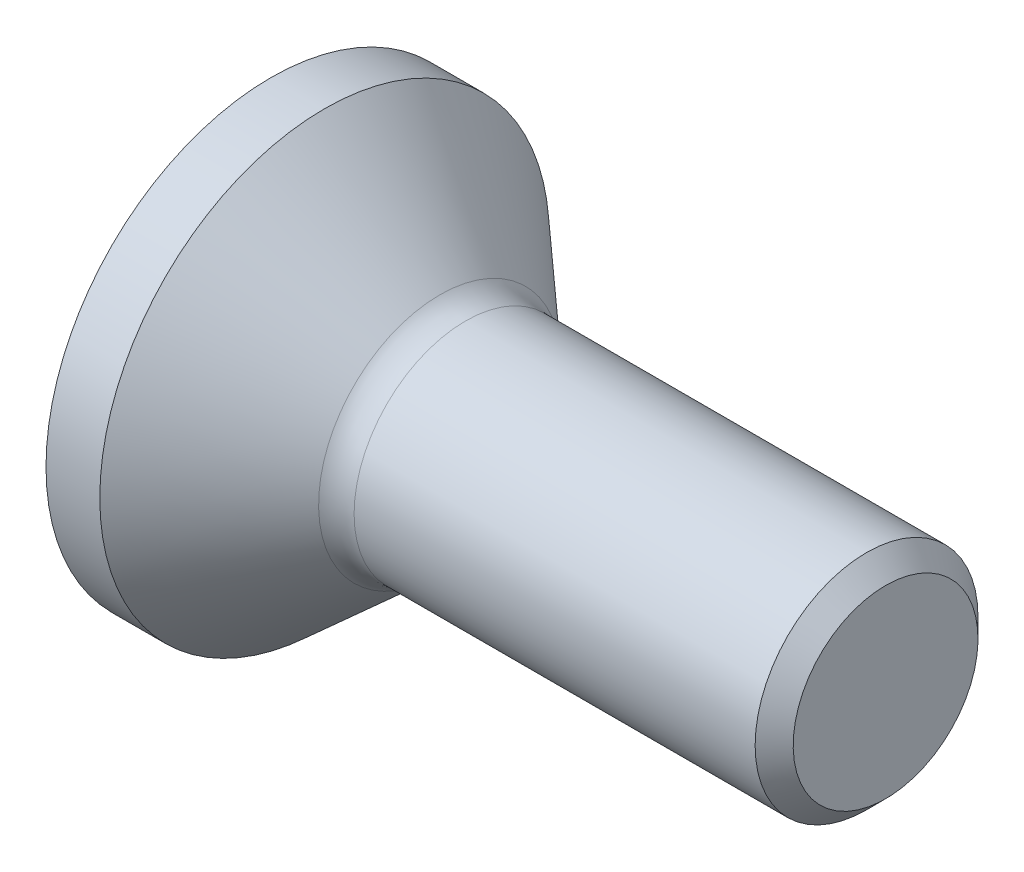
SolidWorks part; units mm, degrees
ref_plane "Front" through (0, 0, 0) normal (0, 0, 1) x (1, 0, 0)
ref_plane "Top" through (0, 0, 0) normal (0, 1, 0) x (1, 0, 0)
ref_plane "Right" through (0, 0, 0) normal (1, 0, 0) x (0, 0, -1)
sketch "Sketch1" plane through (0, 0, 0) normal (0, 0, 1) x (1, 0, 0)
  line L0 (2.5341, 1.45) -> (7.7525, 1.45)
  line L1 (7.7525, 1.45) -> (8, 1.2025)
  line L2 (8, 1.2025) -> (8, 0)
  line L3 (2.2, 1.578) -> (0.7, 2.925)
  line L4 (0.7, 2.925) -> (0, 2.925)
  line L5 (0, 2.925) -> (0, 0)
  line L6 (0, 0) -> (8, 0)
  line L7 (0, 0) -> (-0.9177, 0) construction
  arc A0 (2.5341, 1.45) -> (2.2, 1.578) centre (2.5341, 1.95) cw
  dimension "D1" = 8
  dimension "D4" = 0.5
  dimension "D2" = 5.85
  dimension "D3" = 0.7
  dimension "D5" = 2.9
  dimension "D6" = 135
  dimension "D7" = 0.35
  dimension "D8" = 2.2
revolve "Revolve1" add sketch "Sketch1" angle 360 about L7
sketch "Sketch2" plane through (0, 0, 0) normal (-1, 0, 0) x (0, 0, 1)
  line L1 (1, 0.5774) -> (0, 1.1547)
  line L2 (0, 1.1547) -> (-1, 0.5774)
  line L3 (-1, 0.5774) -> (-1, -0.5774)
  line L4 (-1, -0.5774) -> (0, -1.1547)
  line L5 (0, -1.1547) -> (1, -0.5774)
  line L6 (1, -0.5774) -> (1, 0.5774)
  circle A0 centre (0, 0) radius 1 construction
  dimension "D1" = 2
extrude "Cut-Extrude1" cut sketch "Sketch2" against normal blind 1.5
